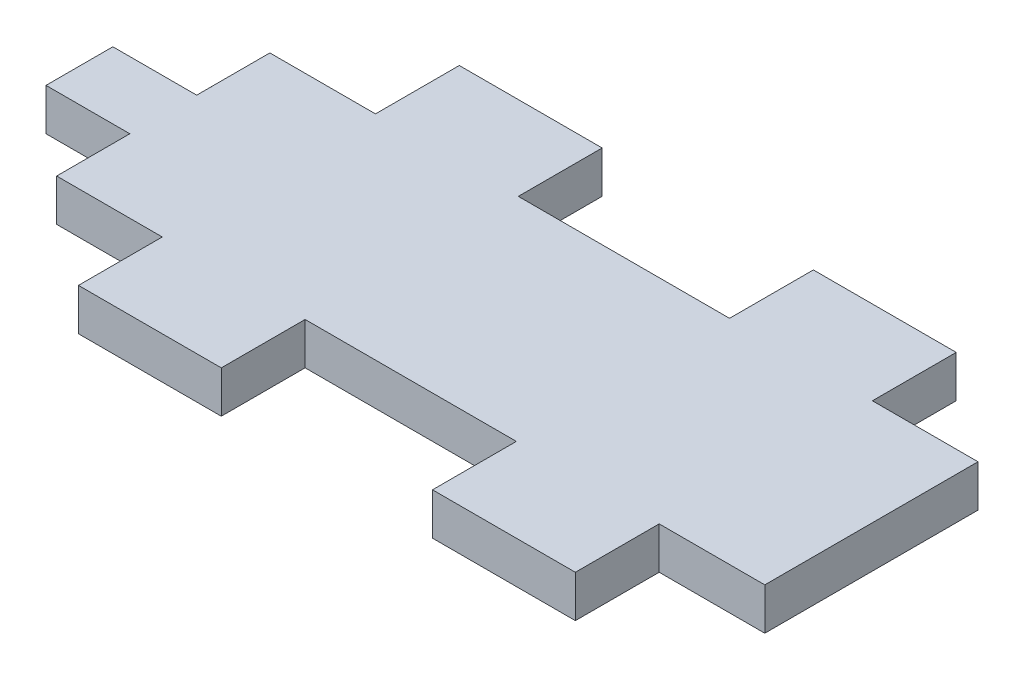
SolidWorks part; units mm, degrees
ref_plane "Front Plane" through (0, 0, 0) normal (0, 0, 1) x (1, 0, 0)
ref_plane "Top Plane" through (0, 0, 0) normal (0, 1, 0) x (1, 0, 0)
ref_plane "Right Plane" through (0, 0, 0) normal (1, 0, 0) x (0, 0, -1)
sketch "Sketch1" plane through (0, 0, 0) normal (0, 1, 0) x (1, 0, 0)
  line L0 (-33.1706, -2.5325) -> (-33.1706, 2.5325)
  line L8 (-33.1706, 2.5325) -> (-26.8206, 2.5325)
  line L10 (-33.1706, -2.5325) -> (-26.8206, -2.5325)
  line L12 (0, 0) -> (0, -8.075) construction
  line L14 (-18.8206, -14.425) -> (-18.8206, -8.075) construction
  line L15 (-8, -14.425) -> (-8, -8.075) construction
  line L16 (-8, -8.075) -> (-18.8206, -8.075) construction
  line L17 (8, -14.425) -> (8, -8.075) construction
  line L18 (8, -8.075) -> (18.8206, -8.075) construction
  line L19 (18.8206, -8.075) -> (18.8206, -14.425) construction
  line L21 (18.8206, 8.075) -> (18.8206, 14.425) construction
  line L23 (8, 14.425) -> (8, 8.075) construction
  line L25 (-8, 14.425) -> (-8, 8.075) construction
  line L27 (-18.8206, 14.425) -> (-18.8206, 8.075) construction
  line L29 (-8, 8.075) -> (8, 8.075)
  line L30 (8, 8.075) -> (8, 14.425)
  line L31 (8, 14.425) -> (18.8206, 14.425)
  line L32 (18.8206, 14.425) -> (18.8206, 8.075)
  line L33 (18.8206, 8.075) -> (26.8206, 8.075)
  line L34 (-8, 8.075) -> (-8, 14.425)
  line L35 (-8, 14.425) -> (-18.8206, 14.425)
  line L36 (-18.8206, 14.425) -> (-18.8206, 8.075)
  line L37 (-18.8206, 8.075) -> (-26.8206, 8.075)
  line L38 (-26.8206, 8.075) -> (-26.8206, 2.5325)
  line L39 (18.8206, -8.075) -> (26.8206, -8.075)
  line L40 (18.8206, -14.425) -> (18.8206, -8.075)
  line L41 (8, -8.075) -> (8, -14.425)
  line L42 (8, -14.425) -> (18.8206, -14.425)
  line L43 (-8, -8.075) -> (8, -8.075)
  line L44 (-8, -8.075) -> (-8, -14.425)
  line L45 (-8, -14.425) -> (-18.8206, -14.425)
  line L46 (-18.8206, -14.425) -> (-18.8206, -8.075)
  line L47 (-26.8206, -8.075) -> (-26.8206, -2.5325)
  line L48 (-18.8206, -8.075) -> (-26.8206, -8.075)
  line L49 (26.8206, -8.075) -> (26.8206, 8.075)
  point P0 (0, 0)
  dimension "D1" = 8
  dimension "D2" = 6.35
  dimension "D3" = 6.35
  dimension "D4" = 5.5425
  dimension "D5" = 10.8206
  dimension "D6" = 16.15
  dimension "D7" = 6.35
  dimension "D8" = 16
  dimension "D9" = 10.8206
  dimension "D10" = 8
  dimension "D11" = 16
  dimension "D12" = 10.8206
  dimension "D13" = 8
  dimension "D14" = 10.8206
  dimension "D15" = 8
extrude "Boss-Extrude1" add sketch "Sketch1" along normal blind 3.175
